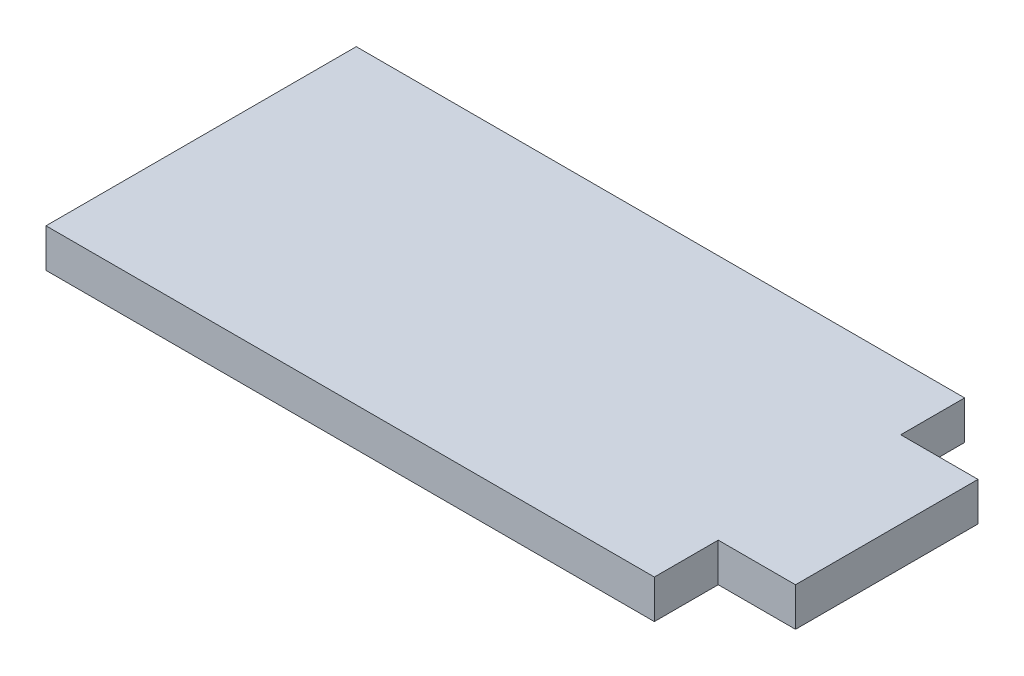
SolidWorks part; units mm, degrees
material "Cedar"
ref_plane "Front Plane" through (0, 0, 0) normal (0, 0, 1) x (1, 0, 0)
ref_plane "Top Plane" through (0, 0, 0) normal (0, 1, 0) x (1, 0, 0)
ref_plane "Right Plane" through (0, 0, 0) normal (1, 0, 0) x (0, 0, -1)
sketch "Sketch1" plane through (0, 0, 0) normal (0, 1, 0) x (1, 0, 0)
  line L0 (-25, 5.25) -> (25, 5.25)
  line L1 (25, 5.25) -> (25, 0)
  line L2 (25, 0) -> (31.35, 0)
  line L3 (31.35, 0) -> (31.35, -15)
  line L4 (31.35, -15) -> (25, -15)
  line L5 (25, -15) -> (25, -20.25)
  line L6 (25, -20.25) -> (-25, -20.25)
  line L7 (-25, -20.25) -> (-25, -15)
  line L8 (-25, -15) -> (-31.35, -15)
  line L9 (-31.35, -15) -> (-31.35, 0)
  line L10 (-31.35, 0) -> (-25, 0)
  line L11 (-25, 0) -> (-25, 5.25)
  line L12 (-25, 0) -> (-25, -15) construction
  point P11 (0, 5.25)
  point P14 (-31.35, -7.5)
  dimension "D1" = 6.35
  dimension "D2" = 15
  dimension "D3" = 50
  dimension "D4" = 25.5
extrude "Boss-Extrude1" add sketch "Sketch1" along normal blind 3.175 contours L11 L12 L7 L6 L5 L4 L3 L2 L1 L0
equation "\"length\"= 25.5mm"
equation "\"w_mach\"= 50mm"
equation "\"w_tab\"= 15mm"
equation "\"t_wood\"= 0.125in"
equation "\"t_side\"= 0.25in"
equation "\"D1@Sketch1\"=\"t_side\""
equation "\"D2@Sketch1\"=\"w_tab\""
equation "\"D3@Sketch1\"=\"w_mach\""
equation "\"D4@Sketch1\"=\"length\""
equation "\"D1@Boss-Extrude1\"=\"t_wood\""
